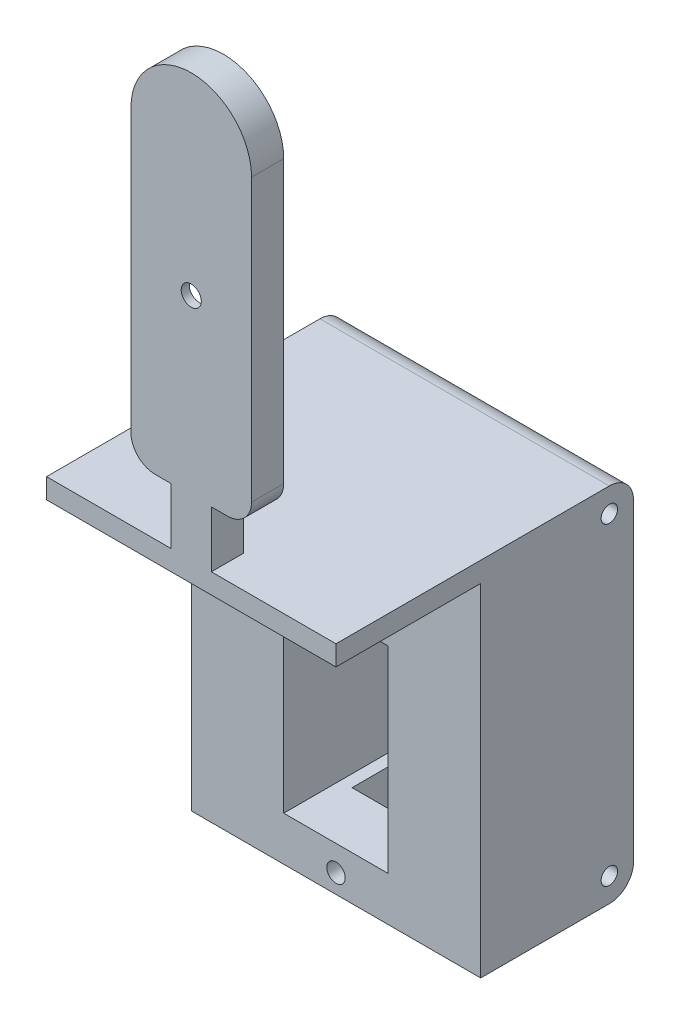
SolidWorks part; units mm, degrees
ref_plane "前基準面" through (0, 0, 0) normal (0, 0, 1) x (1, 0, 0)
ref_plane "上基準面" through (0, 0, 0) normal (0, 1, 0) x (1, 0, 0)
ref_plane "右基準面" through (0, 0, 0) normal (1, 0, 0) x (0, 0, -1)
sketch "草圖1" plane through (0, 0, 0) normal (0, 0, 1) x (1, 0, 0)
  line L0 (0, 62.5) -> (0, 10) construction
  line L1 (7.5, 17) -> (7.5, 55)
  line L3 (-7.5, 17) -> (-7.5, 55)
  line L4 (2.5, 10) -> (-2.5, 10)
  line L6 (-2.5, 15) -> (-2.5, 10)
  line L7 (2.5, 15) -> (2.5, 10)
  line L9 (-7.5, 17) -> (-2.5, 17)
  line L10 (-2.5, 17) -> (-2.5, 15)
  line L11 (2.5, 17) -> (2.5, 15)
  line L12 (7.5, 17) -> (2.5, 17)
  arc A0 (7.5, 55) -> (-7.5, 55) centre (0, 55) ccw
  dimension "D1" = 2
  dimension "D2" = 7.5
  dimension "D4" = 5
extrude "填料-伸長1" add sketch "草圖1" along normal blind 4
sketch "草圖3" plane through (0, 0, 0) normal (0, 0, 1) x (1, 0, 0)
  line L0 (0, 0) -> (0, 18.8578) construction
  line L1 (7.5, 55) -> (-7.5, 55) construction
  line L2 (7.5, 15) -> (-7.5, 15) construction
  line L3 (7.5, 17) -> (7.5, 55) construction
  line L4 (-7.5, 55) -> (-7.5, 17) construction
  line L5 (2.5, 10) -> (-2.5, 10) construction
  line L6 (7.5, 38.5) -> (5, 38.5) construction
  line L7 (5, 38.5) -> (2.1147, 20.658)
  line L8 (5, 38.5) -> (2.1328, 56)
  line L9 (-2.1328, 56) -> (-5, 38.5)
  line L10 (-5, 38.5) -> (-2.1422, 21)
  line L12 (-5, 38.5) -> (-7.5, 38.5) construction
  arc A1 (-4.7386, 40.0956) -> (-4.7403, 36.9094) centre (0, 38.5) ccw
  arc A2 (-2.1422, 21) -> (2.1147, 20.658) centre (0, 21) ccw
  arc A3 (-2.1328, 56) -> (2.1328, 56) centre (0, 56) cw
  arc A4 (4.7452, 36.9241) -> (4.7386, 40.0956) centre (0, 38.5) ccw
  dimension "D4" = 10
  dimension "D5" = 6
  dimension "D1" = 35
  dimension "D2" = 4.2656
  dimension "D3" = 4.257
  dimension "D6" = 5
extrude "除料-伸長1" cut sketch "草圖3" along normal blind 3 contours A3 L9 L10 A2 L7 L8
sketch "草圖5" plane through (0, 0, 0) normal (0, 0, 1) x (1, 0, 0)
  line L0 (5, 38.5) -> (-5, 38.5) construction
  circle A0 centre (0, 38.5) radius 1.25
  dimension "D1" = 2.5
extrude "除料-伸長2" cut sketch "草圖5" along normal blind 12.4
ref_plane "平面1" through (0, -35, 0) normal (0, 1, 0) x (1, 0, 0)
sketch "草圖13" plane through (0, 0, 4) normal (0, 0, 1) x (1, 0, 0)
  line L0 (0, 10) -> (0, -4.3971) construction
  line L1 (2.5, 10) -> (-2.5, 10) construction
  line L3 (-18, 10) -> (18, 10)
  line L4 (-18, 10) -> (-18, -35)
  line L5 (-18, -35) -> (18, -35)
  line L6 (18, 10) -> (18, -35)
  dimension "D1" = 45
  dimension "D2" = 45
  dimension "D3" = 18
  dimension "D4" = 18
ref_plane "平面2" through (0, 0, 4) normal (0, 0, 1) x (1, 0, 0)
extrude "填料-伸長2" add sketch "草圖13" against normal blind 37
sketch "草圖14" plane through (0, 0, 4) normal (0, 0, -1) x (-1, 0, 0)
  line L0 (0, 10) -> (0, -35) construction
  line L1 (-2.5, 10) -> (2.5, 10) construction
  line L2 (18, -35) -> (-18, -35) construction
  line L4 (-6.5, -5) -> (6.5, -5)
  line L5 (-6.5, -5) -> (-6.5, -29.5)
  line L6 (-6.5, -29.5) -> (6.5, -29.5)
  line L7 (6.5, -5) -> (6.5, -29.5)
  point P10 (0, -12.5)
  dimension "D1" = 6.5
  dimension "D2" = 6.5
  dimension "D3" = 24.5
  dimension "D4" = 5.5
ref_plane "平面4" through (0, 0, 4) normal (0, 0, 1) x (1, 0, 0)
extrude "除料-伸長3" cut sketch "草圖14" along normal blind 35
sketch "草圖15" plane through (0, 0, 4) normal (0, 0, 1) x (1, 0, 0)
  line L0 (0, -5) -> (0, -22.6416) construction
  line L1 (-6.5, -5) -> (6.5, -5) construction
  line L2 (0, -1.85) -> (0, -32.65) construction
  line L4 (6.5, -29.5) -> (-6.5, -29.5) construction
  circle A0 centre (0, -1.85) radius 1.15
  circle A1 centre (0, -32.65) radius 1.15
  dimension "D1" = 2.3
  dimension "D2" = 2.3
  dimension "D3" = 2
  dimension "D4" = 2
extrude "除料-伸長4" cut sketch "草圖15" against normal blind 31
ref_plane "平面5" through (0, -35, 0) normal (0, -1, 0) x (-1, 0, 0)
sketch "草圖16" plane through (0, -35, 0) normal (0, -1, 0) x (-1, 0, 0)
  line L0 (0, 33) -> (0, 0) construction
  line L1 (18, 33) -> (-18, 33) construction
  line L3 (-5, 29) -> (5, 29)
  line L4 (-5, 29) -> (-5, 21)
  line L5 (-5, 21) -> (5, 21)
  line L6 (5, 29) -> (5, 21)
  dimension "D1" = 10
  dimension "D2" = 4
  dimension "D3" = 8
  dimension "D4" = 5
extrude "除料-伸長5" cut sketch "草圖16" against normal blind 8
sketch "草圖17" plane through (0, 0, 4) normal (0, 0, 1) x (1, 0, 0)
  line L0 (-18, 10) -> (-18, -35) construction
  line L1 (-18, 7.5) -> (18, 7.5)
  line L2 (-18, 7.5) -> (-18, -35)
  line L3 (-18, -35) -> (18, -35)
  line L4 (18, 7.5) -> (18, -35)
  line L5 (-10.45, -35) -> (10.45, -35) construction
  line L6 (18, -35) -> (18, 10) construction
  line L7 (2.5, 10) -> (-2.5, 10) construction
  dimension "D1" = 2.5
extrude "除料-伸長6" cut sketch "草圖17" against normal blind 18
sketch "草圖23" plane through (-18, 0, 0) normal (-1, 0, 0) x (0, 0, 1)
  line L0 (-33, 10) -> (-33, -35) construction
  line L1 (-33, 10) -> (4, 10) construction
  line L2 (-10.45, -35) -> (10.45, -35) construction
  circle A0 centre (-30, 7) radius 1.025
  circle A1 centre (-30, -32) radius 1.025
  dimension "D5" = 2.05
  dimension "D6" = 2.05
  dimension "D1" = 3
  dimension "D2" = 3
  dimension "D3" = 3
  dimension "D4" = 3
extrude "除料-伸長7" cut sketch "草圖23" against normal blind 5
sketch "草圖24" plane through (18, 0, 0) normal (1, 0, 0) x (0, 0, -1)
  line L0 (33, 10) -> (-4, 10) construction
  line L1 (33, -35) -> (33, 10) construction
  line L2 (-10.45, -35) -> (10.45, -35) construction
  circle A0 centre (30, 7) radius 1.025
  circle A1 centre (30, -32) radius 1.025
  dimension "D5" = 2.05
  dimension "D6" = 2.05
  dimension "D1" = 3
  dimension "D2" = 3
  dimension "D3" = 3
  dimension "D4" = 3
extrude "除料-伸長8" cut sketch "草圖24" against normal blind 5
fillet "圓角1" radius 3 1 edges at (7.5, 17, 2)
fillet "圓角2" radius 3 1 edges at (-7.5, 17, 2)
fillet "圓角3" radius 3 1 edges at (0, 10, -33)
fillet "圓角4" radius 3 1 edges at (0, -35, -33)
